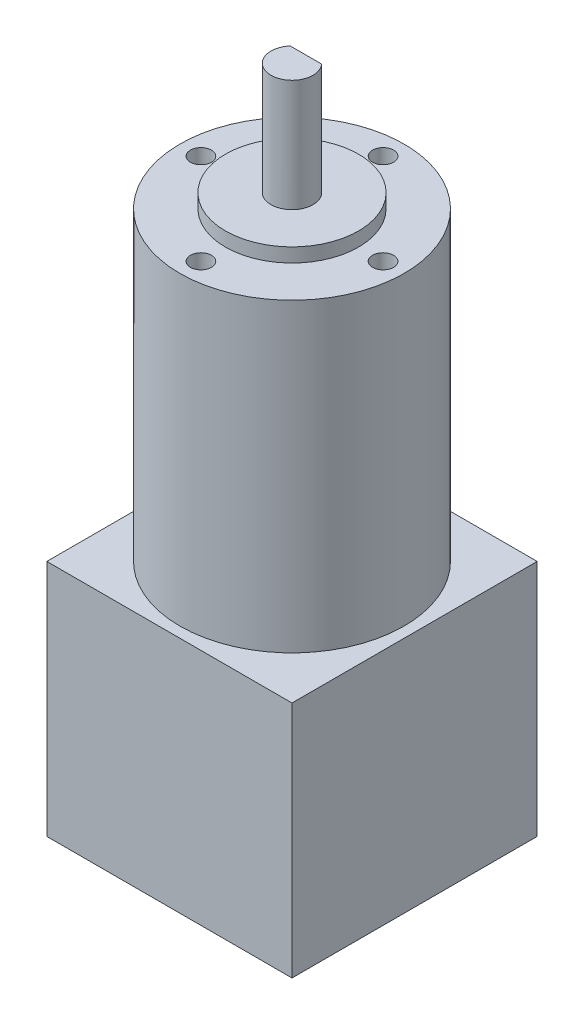
SolidWorks part; units mm, degrees
ref_plane "Front Plane" through (0, 0, 0) normal (0, 0, 1) x (1, 0, 0)
ref_plane "Top Plane" through (0, 0, 0) normal (0, 1, 0) x (1, 0, 0)
ref_plane "Right Plane" through (0, 0, 0) normal (1, 0, 0) x (0, 0, -1)
sketch "Sketch1" plane through (0, 0, 0) normal (0, 1, 0) x (1, 0, 0)
  line L1 (-17.5, -17.5) -> (17.5, -17.5)
  line L2 (-17.5, -17.5) -> (-17.5, 17.5)
  line L3 (-17.5, 17.5) -> (17.5, 17.5)
  line L4 (17.5, -17.5) -> (17.5, 17.5)
  line L5 (-17.5, -17.5) -> (17.5, 17.5) construction
  line L6 (-17.5, 17.5) -> (17.5, -17.5) construction
  point P0 (0, 0)
  dimension "D1" = 35
  dimension "D2" = 35
extrude "Boss-Extrude1" add sketch "Sketch1" along normal blind 34
sketch "Sketch2" plane through (0, 34, 0) normal (0, 1, 0) x (1, 0, 0)
  circle A0 centre (0, 0) radius 16
  dimension "D1" = 32
extrude "Boss-Extrude2" add sketch "Sketch2" along normal blind 43.6
sketch "Sketch3" plane through (0, 77.6, 0) normal (0, 1, 0) x (1, 0, 0)
  circle A0 centre (0, 0) radius 9.5
  dimension "D1" = 19
extrude "Boss-Extrude3" add sketch "Sketch3" along normal blind 2
sketch "Sketch4" plane through (0, 79.6, 0) normal (0, 1, 0) x (1, 0, 0)
  circle A0 centre (0, 0) radius 3
  dimension "D1" = 6
extrude "Boss-Extrude4" add sketch "Sketch4" along normal blind 16
sketch "Sketch5" plane through (0, 95.6, 0) normal (0, 1, 0) x (1, 0, 0)
  line L1 (2.2361, 2) -> (-2.2361, 2)
  arc A0 (2.2361, 2) -> (-2.2361, 2) centre (0, 0) ccw
  point P7 (0, 2)
  dimension "D1" = 6
  dimension "D2" = 4.4721
extrude "Cut-Extrude1" cut sketch "Sketch5" against normal blind 12
sketch "Sketch6" plane through (0, 77.6, 0) normal (0, 1, 0) x (1, 0, 0)
  circle A0 centre (0, 0) radius 13 construction
  circle A1 centre (0, 13) radius 1.5
  circle A2 centre (13, 0) radius 1.5
  circle A5 centre (-13, 0) radius 1.5
  circle A6 centre (0, -13) radius 1.5
  dimension "D1" = 26
  dimension "D2" = 3
extrude "Cut-Extrude2" cut sketch "Sketch6" against normal blind 7
